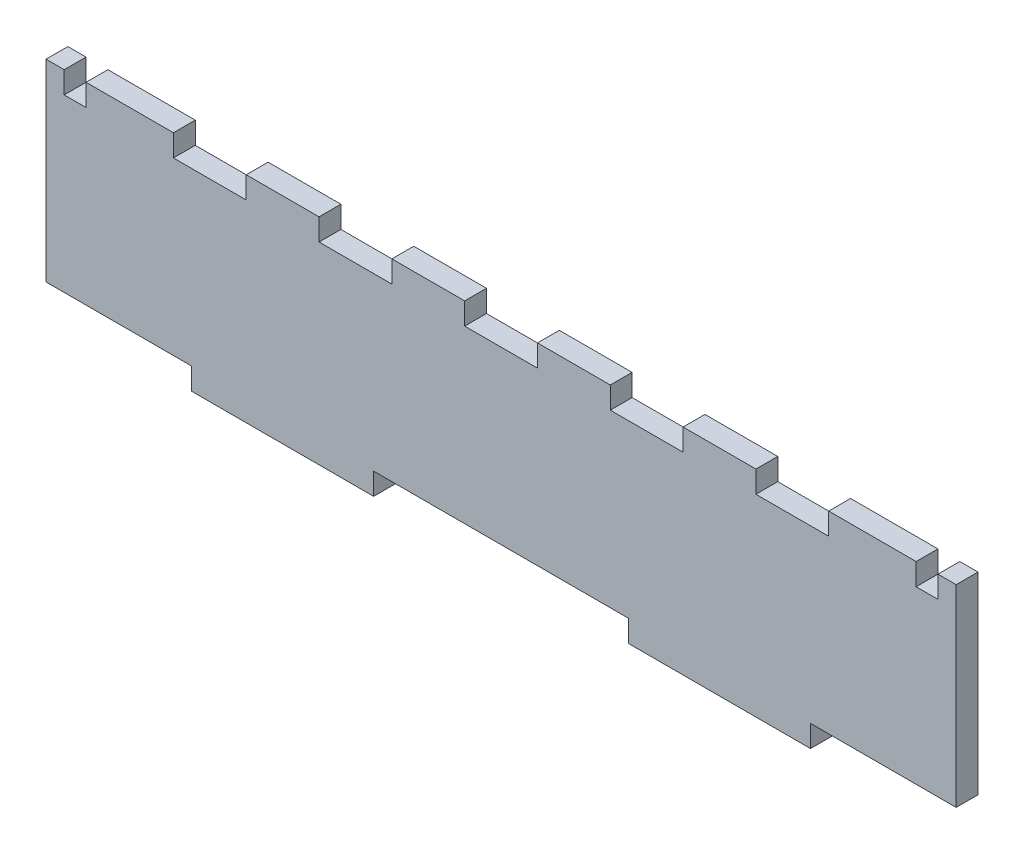
SolidWorks part; units mm, degrees
ref_plane "Front Plane" through (0, 0, 0) normal (0, 0, 1) x (1, 0, 0)
ref_plane "Top Plane" through (0, 0, 0) normal (0, 1, 0) x (1, 0, 0)
ref_plane "Right Plane" through (0, 0, 0) normal (1, 0, 0) x (0, 0, -1)
sketch "Sketch1" plane through (0, 0, 0) normal (0, 0, 1) x (1, 0, 0)
  line L1 (-125, -29.5) -> (125, -29.5)
  line L2 (-125, -29.5) -> (-125, 29.5)
  line L3 (-125, 29.5) -> (125, 29.5)
  line L4 (125, -29.5) -> (125, 29.5)
  line L5 (-125, -29.5) -> (125, 29.5) construction
  line L6 (-125, 29.5) -> (125, -29.5) construction
  line L7 (-125, -29.5) -> (-85, -29.5)
  line L8 (-125, -29.5) -> (-125, -23.5)
  line L9 (-125, -23.5) -> (-85, -23.5)
  line L10 (-85, -29.5) -> (-85, -23.5)
  line L11 (125, -29.5) -> (85, -29.5)
  line L12 (125, -29.5) -> (125, -23.5)
  line L13 (125, -23.5) -> (85, -23.5)
  line L14 (85, -29.5) -> (85, -23.5)
  line L15 (-35, -29.5) -> (35, -29.5)
  line L16 (-35, -29.5) -> (-35, -23.5)
  line L17 (-35, -23.5) -> (35, -23.5)
  line L18 (35, -29.5) -> (35, -23.5)
  point P0 (0, 0)
  point P16 (0, -23.5)
  point P17 (0, -29.5)
  dimension "D1" = 6
  dimension "D2" = 6
  dimension "D3" = 6
  dimension "D4" = 40
  dimension "D5" = 40
  dimension "D6" = 250
  dimension "D7" = 70
  dimension "D8" = 59
extrude "Boss-Extrude1" add sketch "Sketch1" along normal blind 6
sketch "Sketch2" plane through (0, 0, 6) normal (0, 0, 1) x (1, 0, 0)
  line L0 (-125, 29.5) -> (125, 29.5) construction
  line L1 (-90, 29.5) -> (-70, 29.5)
  line L2 (-90, 29.5) -> (-90, 23.5)
  line L3 (-90, 23.5) -> (-70, 23.5)
  line L4 (-70, 29.5) -> (-70, 23.5)
  line L5 (-50, 23.5) -> (-30, 23.5)
  line L6 (-30, 29.5) -> (-30, 23.5)
  line L7 (-50, 29.5) -> (-30, 29.5)
  line L8 (-50, 29.5) -> (-50, 23.5)
  line L9 (-10, 23.5) -> (10, 23.5)
  line L10 (10, 29.5) -> (10, 23.5)
  line L11 (-10, 29.5) -> (10, 29.5)
  line L12 (-10, 29.5) -> (-10, 23.5)
  line L13 (30, 23.5) -> (50, 23.5)
  line L14 (50, 29.5) -> (50, 23.5)
  line L15 (30, 29.5) -> (50, 29.5)
  line L16 (30, 29.5) -> (30, 23.5)
  line L17 (70, 23.5) -> (90, 23.5)
  line L18 (90, 29.5) -> (90, 23.5)
  line L19 (70, 29.5) -> (90, 29.5)
  line L20 (70, 29.5) -> (70, 23.5)
  line L22 (-120, 29.5) -> (-114, 29.5)
  line L23 (-120, 29.5) -> (-120, 23.5)
  line L24 (-120, 23.5) -> (-114, 23.5)
  line L25 (-114, 29.5) -> (-114, 23.5)
  line L26 (114, 29.5) -> (120, 29.5)
  line L27 (114, 29.5) -> (114, 23.5)
  line L28 (114, 23.5) -> (120, 23.5)
  line L29 (120, 29.5) -> (120, 23.5)
  dimension "D1" = 6
  dimension "D2" = 35
  dimension "D3" = 20
  dimension "D5" = 5
  dimension "D6" = 5
  dimension "D7" = 6
  dimension "D8" = 6
  dimension "D4" = 5
extrude "Cut-Extrude1" cut sketch "Sketch2" against normal up to next
equation "\"Material Thickness\"= 6"
equation "\"D1@Sketch1\"=\"Material Thickness\""
equation "\"D2@Sketch1\"=\"Material Thickness\""
equation "\"D3@Sketch1\"=\"Material Thickness\""
equation "\"D1@Boss-Extrude1\"=\"Material Thickness\""
equation "\"D1@Sketch2\"=\"Material Thickness\""
equation "\"D7@Sketch2\"=\"Material Thickness\""
equation "\"D8@Sketch2\"=\"Material Thickness\""
equation "\"D8@Sketch1\"= 47mm + ( 2 * \"Material Thickness\" )"
